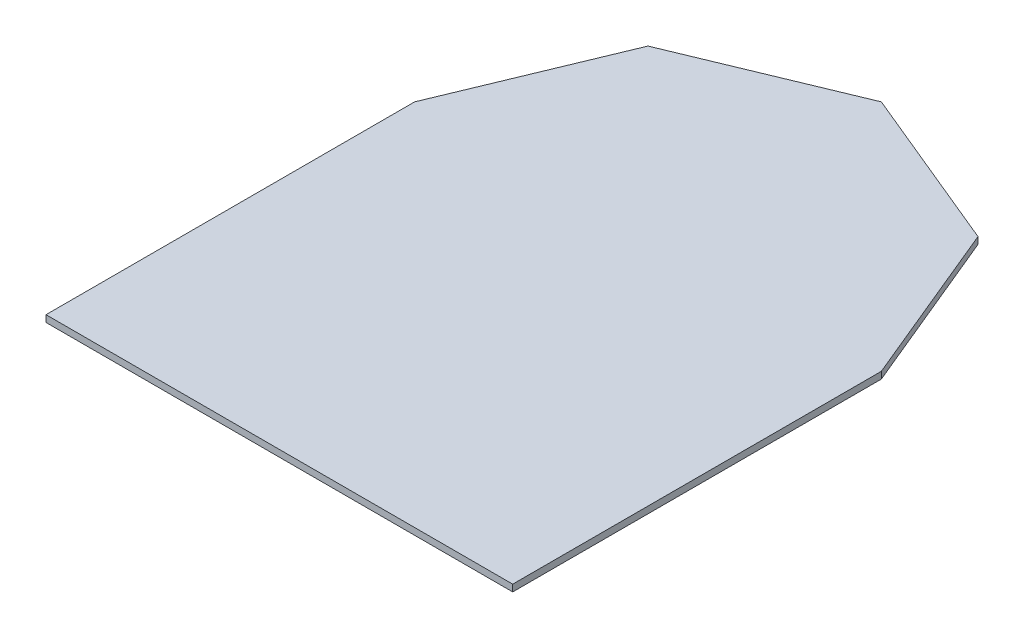
SolidWorks part; units mm, degrees
ref_plane "Front Plane" through (0, 0, 0) normal (0, 0, 1) x (1, 0, 0)
ref_plane "Top Plane" through (0, 0, 0) normal (0, 1, 0) x (1, 0, 0)
ref_plane "Right Plane" through (0, 0, 0) normal (1, 0, 0) x (0, 0, -1)
sketch "Sketch1" plane through (0, 0, 0) normal (0, 1, 0) x (1, 0, 0)
  line L1 (0, 0) -> (172.5, 0)
  line L2 (0, 0) -> (0, 136.25)
  line L3 (0, 136.25) -> (172.5, 136.25) construction
  line L4 (172.5, 0) -> (172.5, 136.25)
  line L9 (172.5, 136.25) -> (147.238, 197.238)
  line L10 (147.238, 197.238) -> (86.25, 222.5)
  line L11 (86.25, 222.5) -> (25.262, 197.238)
  line L12 (25.262, 197.238) -> (0, 136.25)
  line L13 (0, 136.25) -> (12.631, 105.756) [skipped]
  line L14 (55.756, 62.631) -> (86.25, 50) [skipped]
  line L15 (116.744, 62.631) -> (147.238, 75.262) [skipped]
  line L16 (159.869, 105.756) -> (172.5, 136.25) [skipped]
  arc A0 (172.5, 136.25) -> (0, 136.25) centre (86.25, 136.25) ccw construction
  circle A1 centre (86.25, 136.25) radius 79.6846 construction
  point P7 (86.25, 222.5)
  dimension "D3" = 159.3692
  dimension "D1" = 172.5
  dimension "D2" = 222.5
extrude "Boss-Extrude1" add sketch "Sketch1" along normal blind 2.5
